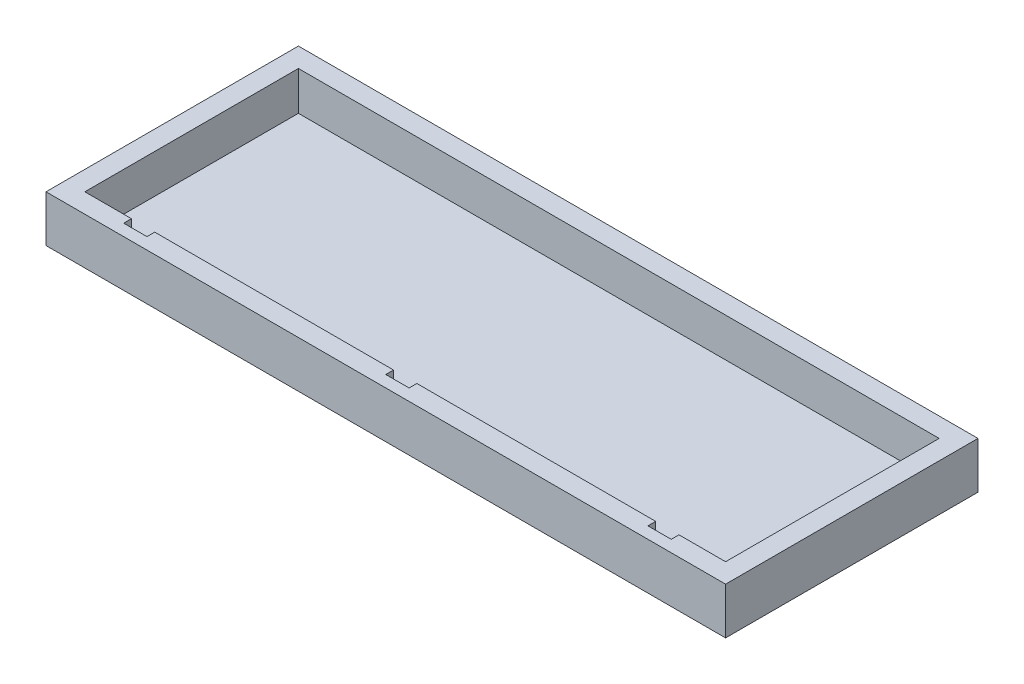
SolidWorks part; units mm, degrees
ref_plane "Front Plane" through (0, 0, 0) normal (0, 0, 1) x (1, 0, 0)
ref_plane "Top Plane" through (0, 0, 0) normal (0, 1, 0) x (1, 0, 0)
ref_plane "Right Plane" through (0, 0, 0) normal (1, 0, 0) x (0, 0, -1)
sketch "Sketch1" plane through (0, 0, 0) normal (0, 1, 0) x (1, 0, 0)
  line L1 (-87.5, -32.5) -> (87.5, -32.5)
  line L2 (-87.5, -32.5) -> (-87.5, 32.5)
  line L3 (-87.5, 32.5) -> (87.5, 32.5)
  line L4 (87.5, -32.5) -> (87.5, 32.5)
  line L5 (-87.5, -32.5) -> (87.5, 32.5) construction
  line L6 (-87.5, 32.5) -> (87.5, -32.5) construction
  point P0 (0, 0)
  point P1 (0, 0)
  dimension "D1" = 175
  dimension "D2" = 65
extrude "Boss-Extrude1" add sketch "Sketch1" along normal blind 12
sketch "Sketch2" plane through (0, 12, 0) normal (0, 1, 0) x (1, 0, 0)
  line L1 (82.5, -27.5) -> (-82.5, -27.5)
  line L2 (82.5, -27.5) -> (82.5, 27.5)
  line L3 (82.5, 27.5) -> (-82.5, 27.5)
  line L4 (-82.5, -27.5) -> (-82.5, 27.5)
  line L5 (82.5, -27.5) -> (-82.5, 27.5) construction
  line L6 (82.5, 27.5) -> (-82.5, -27.5) construction
  point P0 (0, 0)
  point P1 (0, 0)
  dimension "D1" = 165
  dimension "D2" = 55
extrude "Cut-Extrude1" cut sketch "Sketch2" against normal blind 10
sketch "Sketch5" plane through (0, 0, 27.5) normal (0, 0, -1) x (-1, 0, 0)
  line L0 (-82.5, 7) -> (82.5, 7) construction
  line L1 (-82.5, 2) -> (-82.5, 12) construction
  line L2 (82.5, 2) -> (82.5, 12) construction
  line L3 (0, 2) -> (0, 12) construction
  line L4 (82.5, 2) -> (-82.5, 2) construction
  line L5 (82.5, 12) -> (-82.5, 12) construction
  line L7 (-3, 12) -> (3, 12)
  line L8 (-3, 12) -> (-3, 2)
  line L9 (-3, 2) -> (3, 2)
  line L10 (3, 12) -> (3, 2)
  line L11 (-3, 12) -> (3, 2) construction
  line L12 (-3, 2) -> (3, 12) construction
  point P12 (0, 7)
  dimension "D1" = 6
extrude "Cut-Extrude2" cut sketch "Sketch5" against normal blind 2
sketch "Sketch6" plane through (0, 0, 27.5) normal (0, 0, -1) x (-1, 0, 0)
  line L0 (-82.5, 7) -> (-67.5, 7) construction
  line L1 (-82.5, 2) -> (-82.5, 12) construction
  line L2 (-3, 12) -> (-82.5, 12) construction
  line L3 (-70.5, 2) -> (-64.5, 2)
  line L4 (-70.5, 2) -> (-70.5, 12)
  line L5 (-70.5, 12) -> (-64.5, 12)
  line L6 (-64.5, 2) -> (-64.5, 12)
  line L7 (-70.5, 2) -> (-64.5, 12) construction
  line L8 (-70.5, 12) -> (-64.5, 2) construction
  dimension "D1" = 15
  dimension "D2" = 6
extrude "Cut-Extrude3" cut sketch "Sketch6" against normal blind 2
sketch "Sketch7" plane through (0, 0, 27.5) normal (0, 0, -1) x (-1, 0, 0)
  line L0 (82.5, 7) -> (67.5, 7) construction
  line L1 (82.5, 12) -> (3, 12) construction
  line L2 (82.5, 2) -> (82.5, 12) construction
  line L3 (64.5, 2) -> (70.5, 2)
  line L4 (64.5, 2) -> (64.5, 12)
  line L5 (64.5, 12) -> (70.5, 12)
  line L6 (70.5, 2) -> (70.5, 12)
  line L7 (64.5, 2) -> (70.5, 12) construction
  line L8 (64.5, 12) -> (70.5, 2) construction
  dimension "D1" = 15
  dimension "D2" = 6
extrude "Cut-Extrude4" cut sketch "Sketch7" against normal blind 2
sketch "Sketch15" plane through (0, 2, 0) normal (0, 1, 0) x (1, 0, 0)
  line L0 (-67.5, -29.5) -> (-67.5, 27.5) construction
  line L1 (-70.5, -29.5) -> (-64.5, -29.5) construction
  line L2 (82.5, 27.5) -> (-82.5, 27.5) construction
